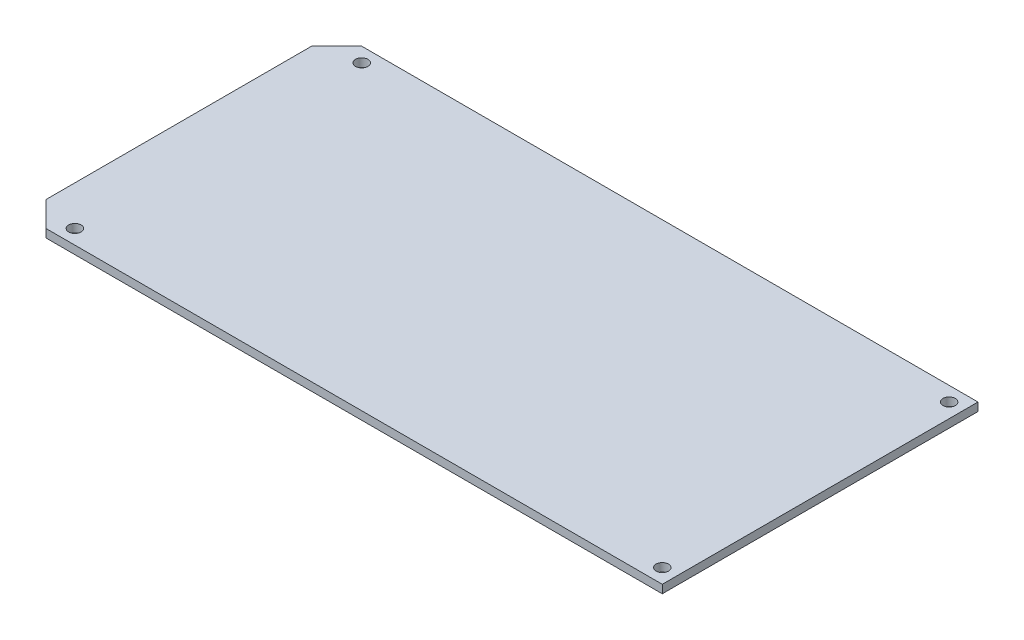
SolidWorks part; units mm, degrees
ref_plane "Front Plane" through (0, 0, 0) normal (0, 0, 1) x (1, 0, 0)
ref_plane "Top Plane" through (0, 0, 0) normal (0, 1, 0) x (1, 0, 0)
ref_plane "Right Plane" through (0, 0, 0) normal (1, 0, 0) x (0, 0, -1)
sketch "Sketch2" plane through (0, 0, 0) normal (0, 1, 0) x (1, 0, 0)
  line L0 (-149.27, 76.47) -> (-155.344, 70.396)
  line L1 (-149.27, 76.47) -> (0, 76.47)
  line L2 (-155.344, 70.396) -> (-155.344, 6.074)
  line L3 (-149.27, 0) -> (0, 0)
  line L4 (0, 76.47) -> (0, 0)
  line L5 (-155.344, 6.074) -> (-149.27, 0)
  line L6 (-145.77, 72.97) -> (-145.77, 3.5) construction
  line L7 (-145.77, 3.5) -> (-3.5, 3.5) construction
  line L8 (-3.5, 3.5) -> (-3.5, 72.97) construction
  line L9 (-145.77, 72.97) -> (-3.5, 72.97) construction
  circle A0 centre (-3.5, 72.97) radius 1.5
  circle A1 centre (-3.5, 3.5) radius 1.5
  circle A2 centre (-145.77, 72.97) radius 1.5
  circle A3 centre (-145.77, 3.5) radius 1.5
  dimension "D7" = 3
  dimension "D8" = 3
  dimension "D9" = 3
  dimension "D10" = 3
  dimension "D1" = 76.47
  dimension "D2" = 45
  dimension "D3" = 45
  dimension "D4" = 8.59
  dimension "D5" = 8.59
  dimension "D6" = 149.27
  dimension "D11" = 3.5
  dimension "D12" = 3.5
  dimension "D13" = 3.5
  dimension "D14" = 3.5
extrude "Boss-Extrude1" add sketch "Sketch2" along normal blind 2
